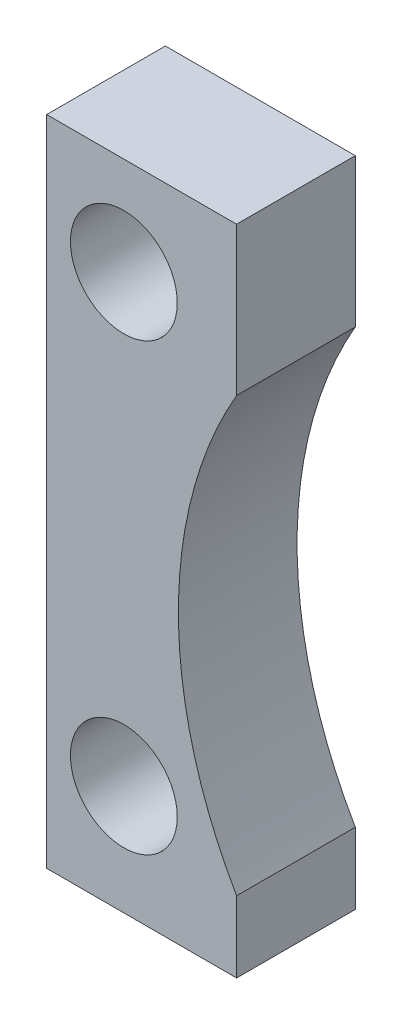
SolidWorks part; units mm, degrees
ref_plane "Front Plane" through (0, 0, 0) normal (0, 0, 1) x (1, 0, 0)
ref_plane "Top Plane" through (0, 0, 0) normal (0, 1, 0) x (1, 0, 0)
ref_plane "Right Plane" through (0, 0, 0) normal (1, 0, 0) x (0, 0, -1)
sketch "Çizim1" plane through (0, 0, 0) normal (0, 0, 1) x (1, 0, 0)
  line L0 (0, 0) -> (0, 110)
  line L1 (0, 110) -> (32, 110)
  line L2 (32, 110) -> (32, 85)
  line L3 (0, 0) -> (32, 0)
  line L4 (32, 0) -> (32, 12)
  arc A0 (32, 12) -> (32, 85) centre (95, 48.5) cw
  dimension "D1" = 110
  dimension "D2" = 32
  dimension "D3" = 25
  dimension "D4" = 12
  dimension "D5" = 95
extrude "Yükseklik-Ekstrüzyon1" add sketch "Çizim1" along normal mid plane 20
sketch "Çizim2" plane through (0, 0, 10) normal (0, 0, 1) x (1, 0, 0)
  line L0 (0, 110) -> (0, 0) construction
  line L1 (32, 110) -> (0, 110) construction
  line L2 (0, 0) -> (32, 0) construction
  circle A0 centre (13, 93.5) radius 9
  circle A1 centre (13, 18.5) radius 9
  dimension "D1" = 18
  dimension "D2" = 13
  dimension "D3" = 16.5
  dimension "D4" = 18.5
  dimension "D5" = 13
extrude "Kes-Ekstrüzyon1" cut sketch "Çizim2" against normal through all
